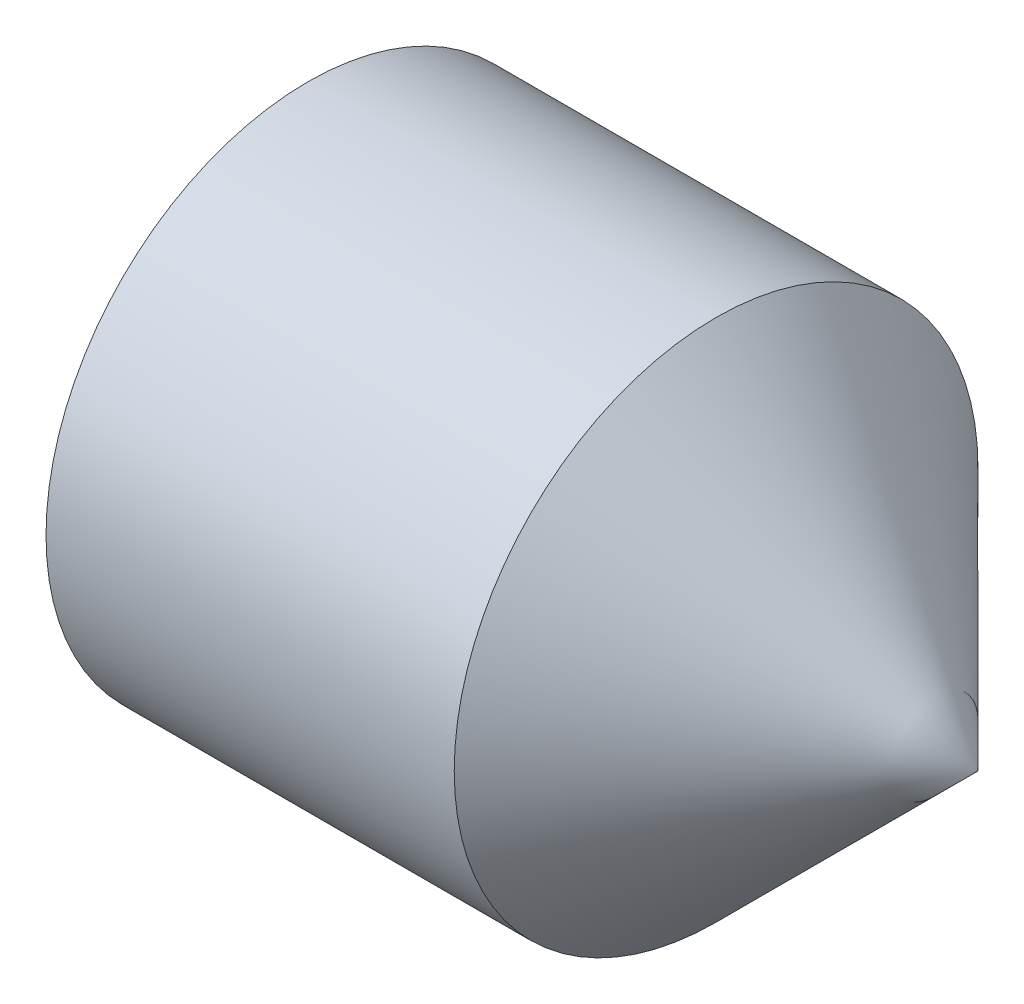
SolidWorks part; units mm, degrees
revolve "BaseBody" add sketch "BodySke" angle 360 about L5
sketch "BodySke" plane through (0, 0, 0) normal (0, 0, 1) x (1, 0, 0)
  line L0 (0, 0) -> (0, 1.2195)
  line L1 (0, 1.2195) -> (0.1619, 1.5)
  line L2 (0.1619, 1.5) -> (2.5, 1.5)
  line L3 (2.5, 1.5) -> (4, 0)
  line L4 (4, 0) -> (0, 0)
  line L5 (-12.7, 0) -> (88.9, 0) construction
  line L6 (2.5, -1.5) -> (4, 0) construction
  line L7 (0.25, 15.875) -> (0.25, -3.175) construction
  line L8 (0, -1.2195) -> (0.1619, -1.5) construction
  dimension "Diameter" = 3
  dimension "Drive_ch_ang" = 60
  dimension "Minor_dia" = 2.439
  dimension "Advance" = 0.5
  dimension "Cone_ang" = 90
  dimension "Length" = 4
cosmetic thread "ThreadCosmetic" [suppressed] parameters "Thread_minor"=2.439
ref_plane "Plane1" through (0, 0, 0) normal (0, 0, 1) x (1, 0, 0)
ref_plane "Plane2" through (0, 0, 0) normal (0, 1, 0) x (1, 0, 0)
ref_plane "Plane3" through (0, 0, 0) normal (1, 0, 0) x (0, 0, -1)
sketch "Sketch2" plane through (0, 0, 0) normal (-1, 0, 0) x (0, 0, 1)
  line L0 (0.433, 0.75) -> (-0.433, 0.75)
  line L1 (-0.433, 0.75) -> (-0.866, 0)
  line L2 (0.433, 0.75) -> (0.866, 0)
  line L3 (0.433, -0.75) -> (0.866, 0)
  line L4 (0.433, -0.75) -> (-0.433, -0.75)
  line L5 (-0.433, -0.75) -> (-0.866, 0)
  dimension "Hex_size" = 1.5
  dimension "D2" = 0.75
  dimension "D3" = 0.75
extrude "Hex" cut sketch "Sketch2" against normal blind 2
sketch "ThdSchSke" plane through (0, 0, 0) normal (0, 0, 1) x (1, 0, 0)
  line L0 (0.1619, -1.2195) -> (-0.0345, -1.5)
  line L1 (0.1619, -1.2195) -> (0.3584, -1.5)
  line L2 (0.3584, -1.5) -> (0.3584, -1.875)
  line L3 (-3.175, 0) -> (5.1513, 0) construction
  line L4 (0.1619, 1.5) -> (0.1619, -1.5) construction
  line L5 (0.3584, -1.875) -> (-0.0345, -1.875)
  line L6 (-0.0345, -1.875) -> (-0.0345, -1.5)
  dimension "Thread_minor" = 2.439
  dimension "Diameter" = 3
revolve "ThreadSchematic" [suppressed] cut sketch "ThdSchSke" angle 360 about L3
pattern_linear "ThdSchPat" [suppressed]
equation "\"D2@Sketch2\" = \"Hex_size@Sketch2\" / 2"
equation "\"D3@Sketch2\" = \"Hex_size@Sketch2\" / 2"
equation "\"Thread_minor@ThreadCosmetic\" = \"Minor_dia@BodySke\""
equation "\"Thread_minor@ThdSchSke\" = \"Thread_minor@ThreadCosmetic\""
equation "\"Diameter@ThdSchSke\" = \"Diameter@BodySke\""
equation "\"Overcut@ThdSchSke\" = \"Diameter@BodySke\" * 1.25"
equation "\"Num_threads@ThdSchPat\" = int( (\"Length@BodySke\" - ( ( ( \"Diameter@BodySke\" - \"Minor_dia@BodySke\" ) * 0.5 ) / tan( \"Drive_ch_ang@BodySke\" * 0.017453292 ) ) - ( ( \"Diameter@BodySke\" * 0.5 ) / tan( \"Cone_ang@BodySke\" * 0.008726646 ) ) ) / \"Advance@BodySke\" + 0.999 )  + 1"
equation "\"Advance@ThdSchPat\" = (\"Length@BodySke\" - ( ( ( \"Diameter@BodySke\" - \"Minor_dia@BodySke\" ) * 0.5 ) / tan( \"Drive_ch_ang@BodySke\" * 0.017453292 ) ) - ( ( \"Diameter@BodySke\" * 0.5 ) / tan( \"Cone_ang@BodySke\" * 0.008726646 ) ) ) /  (\"Num_threads@ThdSchPat\" - 1) 'relax it"
equation "' \"Num_threads@ThdSchPat\" = \"Num_threads@ThdSchPat\" - sgn( \"Num_threads@ThdSchPat\" - 1) '---chamfered tips only---"
